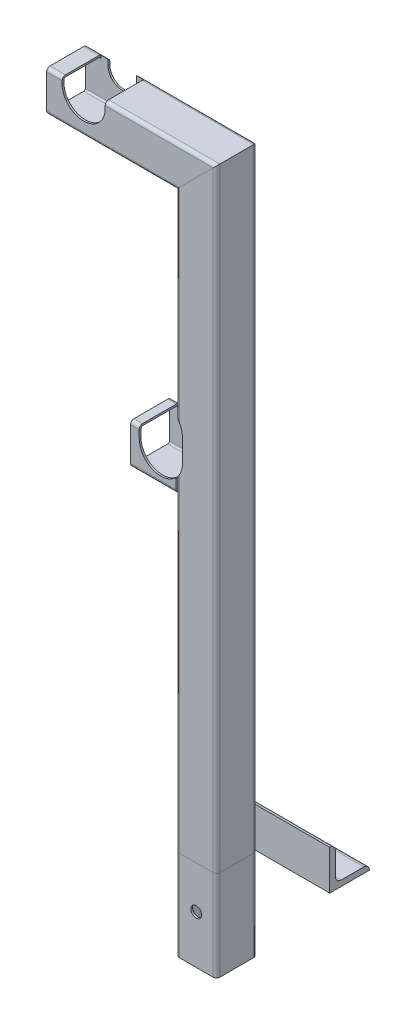
SolidWorks part; units mm, degrees
ref_plane "Front Plane" through (0, 0, 0) normal (0, 0, 1) x (1, 0, 0)
ref_plane "Top Plane" through (0, 0, 0) normal (0, 1, 0) x (1, 0, 0)
ref_plane "Right Plane" through (0, 0, 0) normal (1, 0, 0) x (0, 0, -1)
sketch "Sketch1" plane through (0, 0, 0) normal (0, 0, 1) x (1, 0, 0)
  line L0 (361.4375, 0) -> (361.4375, 524)
  line L1 (361.4375, 524) -> (229.3375, 524)
  line L2 (361.4375, 0) -> (361.4375, -80)
  line L3 (343.5375, 157.0549) -> (343.5375, -80) construction
  line L4 (348.3, 157.0549) -> (348.3, -80) construction
  line L5 (361.4375, 157.0549) -> (361.4375, -80) construction
  line L6 (361.4375, 291.4) -> (303.5375, 291.4)
  dimension "D1" = 524
  dimension "D2" = 80
  dimension "D3" = 132.1
  dimension "D4" = 4.7625
  dimension "D5" = 17.9
  dimension "D6" = 348.3
  dimension "D7" = 57.9
  dimension "D8" = 291.4
other "Structural MemberMain"
ref_plane "Plane1" through (361.4375, 0, 0) normal (0, 1, 0) x (-1, 0, 0)
sketch "Sketch11" plane through (361.4375, 0, 0) normal (0, 1, 0) x (-1, 0, 0)
  line L0 (-14.9, 16.3) -> (14.9, 16.3)
  line L1 (-14.9, 17.9) -> (14.9, 17.9)
  line L2 (-17.9, 14.9) -> (-17.9, -14.9)
  line L3 (-14.9, -17.9) -> (14.9, -17.9)
  line L4 (17.9, 14.9) -> (17.9, -14.9)
  line L5 (-17.9, 17.9) -> (17.9, -17.9) construction
  line L6 (-17.9, -17.9) -> (17.9, 17.9) construction
  line L7 (16.3, 14.9) -> (16.3, -14.9)
  line L8 (-14.9, -16.3) -> (14.9, -16.3)
  line L9 (-16.3, 14.9) -> (-16.3, -14.9)
  arc A0 (-17.9, -14.9) -> (-14.9, -17.9) centre (-14.9, -14.9) ccw
  arc A1 (14.9, -17.9) -> (17.9, -14.9) centre (14.9, -14.9) ccw
  arc A2 (17.9, 14.9) -> (14.9, 17.9) centre (14.9, 14.9) ccw
  arc A3 (-14.9, 17.9) -> (-17.9, 14.9) centre (-14.9, 14.9) ccw
  arc A4 (16.3, 14.9) -> (14.9, 16.3) centre (14.9, 14.9) ccw
  arc A5 (14.9, -16.3) -> (16.3, -14.9) centre (14.9, -14.9) ccw
  arc A6 (-16.3, -14.9) -> (-14.9, -16.3) centre (-14.9, -14.9) ccw
  arc A7 (-14.9, 16.3) -> (-16.3, 14.9) centre (-14.9, 14.9) ccw
  point P0 (0, 0)
  point P30 (0, 0)
  dimension "D3" = 3
  dimension "D1" = 35.8
  dimension "D2" = 35.8
  dimension "D4" = 1.6
sketch "Sketch12" plane through (0, 0, 0) normal (0, 0, 1) x (1, 0, 0)
  line L1 (262, 536.7) -> (262, 547.1) construction
  line L2 (249.3, 536.7) -> (249.3, 547.1)
  line L3 (274.7, 536.7) -> (274.7, 547.1)
  line L4 (361.4375, 524) -> (229.3375, 524) construction
  line L5 (229.3375, 541.9) -> (379.3375, 541.9) construction
  arc A0 (249.3, 536.7) -> (274.7, 536.7) centre (262, 536.7) ccw
  arc A1 (274.7, 547.1) -> (249.3, 547.1) centre (262, 547.1) ccw
  point P2 (262, 541.9)
  dimension "D1" = 25.4
  dimension "D2" = 262
extrude "Cut-ExtrudeTopRailGuide" cut sketch "Sketch12" against normal through all and the other way through all
sketch "Sketch13" plane through (0, 0, 0) normal (0, 1, 0) x (1, 0, 0)
  line L0 (343.5375, 17.9) -> (443.5375, 17.9)
  line L1 (343.5375, -14.9) -> (343.5375, 14.9) construction
  line L2 (274.7, 17.9) -> (376.3375, 17.9) construction
  point P4 (393.5375, 17.9)
  dimension "D1" = 100
other "Structural MemberAngle"
ref_plane "Plane2" through (343.5375, 0, -17.9) normal (1, 0, 0) x (0, 0, -1)
sketch "Sketch14" plane through (343.5375, 0, -17.9) normal (1, 0, 0) x (0, 0, -1)
  line L0 (0, 0) -> (0, 35)
  line L1 (0, 17.5) -> (5, 17.5) construction
  line L2 (5, 30) -> (5, 10)
  line L3 (10, 5) -> (30, 5)
  line L4 (17.5, 5) -> (17.5, 0) construction
  line L5 (35, 0) -> (0, 0)
  arc A0 (35, 0) -> (30, 5) centre (30, 0) ccw
  arc A1 (0, 35) -> (5, 30) centre (0, 30) cw
  arc A2 (10, 5) -> (5, 10) centre (10, 10) cw
  point P10 (17.5, 0)
  point P14 (0, 17.5)
  point P15 (5, 17.5)
  point P16 (17.5, 5)
  point P17 (5, 35)
  point P18 (35, 5)
  point P21 (0, 0)
  dimension "D2" = 5
  dimension "D3" = 35
  dimension "Radius_1" = 5
  dimension "D1" = 5
sketch "Sketch15" plane through (0, 0, 0) normal (0, 1, 0) x (1, 0, 0)
  line L0 (343.5375, 17.9) -> (443.5375, 17.9) construction
  line L2 (-65.8005, 37.9) -> (724.4755, 37.9) construction
  line L4 (0, 28.933) -> (0, -28.933) construction
  circle A0 centre (312.8, 37.9) radius 4.7625 construction
  circle A1 centre (348.3, 37.9) radius 5.0441 construction
  circle A2 centre (375, 37.9) radius 4.7625
  circle A3 centre (410, 37.9) radius 4.7625
  point P7 (329.3375, 37.9)
  point P16 (0, 0)
  dimension "D2" = 9.525
  dimension "D1" = 20
  dimension "D3" = 348.3
  dimension "D4" = 35.5
  dimension "D5" = 35
  dimension "D6" = 410
extrude "Cut-ExtrudeMountingHoles" cut sketch "Sketch15" along normal through all
sketch "Sketch16" plane through (0, 0, 0) normal (0, 0, 1) x (1, 0, 0)
  line L4 (281.05, 536.7) -> (281.05, 547.1)
  line L5 (242.95, 547.1) -> (242.95, 536.7)
  line L6 (281.05, 536.7) -> (281.05, 547.1)
  line L7 (242.95, 547.1) -> (242.95, 536.7)
  arc A4 (242.95, 536.7) -> (281.05, 536.7) centre (262, 536.7) ccw
  arc A5 (281.05, 547.1) -> (242.95, 547.1) centre (262, 547.1) ccw
  arc A6 (242.95, 536.7) -> (281.05, 536.7) centre (262, 536.7) ccw
  arc A7 (281.05, 547.1) -> (242.95, 547.1) centre (262, 547.1) ccw
  dimension "D1" = 6.35
extrude "Cut-ExtrudeEnlargeRailGuide" cut sketch "Sketch16" against normal up to surface and the other way through all up to face at (278.6938, 529.3125, -16.3)
sketch "Sketch17" plane through (0, 0, -17.9) normal (0, 0, 1) x (1, 0, 0)
  line L0 (330.2, 304.1) -> (330.2, 314.5) construction
  line L1 (317.5, 304.1) -> (317.5, 314.5)
  line L2 (342.9, 304.1) -> (342.9, 314.5)
  line L3 (303.5375, 309.3) -> (343.5375, 309.3) construction
  line L4 (361.4375, 291.4) -> (303.5375, 291.4) construction
  arc A0 (317.5, 304.1) -> (342.9, 304.1) centre (330.2, 304.1) ccw
  arc A1 (342.9, 314.5) -> (317.5, 314.5) centre (330.2, 314.5) ccw
  point P2 (330.2, 309.3)
  dimension "D1" = 25.4
  dimension "D2" = 12.7
  dimension "D3" = 330.2
extrude "Cut-Extrude1" cut sketch "Sketch17" along normal through all
sketch "Sketch18" plane through (0, 0, 17.9) normal (0, 0, 1) x (1, 0, 0)
  line L3 (330.2, 319.3) -> (330.2, 299.3) construction
  line L4 (349.3, 319.3) -> (349.3, 299.3)
  line L7 (311.1, 319.3) -> (311.1, 299.3)
  line L8 (330.2, 304.1) -> (330.2, 314.5) construction
  line L9 (303.5375, 309.3) -> (317.5, 309.3) construction
  arc A3 (349.3, 319.3) -> (311.1, 319.3) centre (330.2, 319.3) ccw
  arc A4 (311.1, 299.3) -> (349.3, 299.3) centre (330.2, 299.3) ccw
  point P2 (330.2, 309.3)
  dimension "D1" = 19.1
  dimension "D2" = 10
extrude "Cut-Extrude2" cut sketch "Sketch18" against normal up to surface (34.2 mm away)
sketch "Sketch19" plane through (0, 0, 17.9) normal (0, 0, 1) x (1, 0, 0)
  line L0 (361.4375, 0) -> (361.4375, -80) construction
  line L1 (343.5375, 0) -> (443.5375, 0) construction
  line L2 (379.3375, 0) -> (379.3375, -80) construction
  circle A0 centre (361.4375, -37.5) radius 4.7625
  dimension "D1" = 9.525
  dimension "D3" = 17.9
  dimension "D2" = 37.5
extrude "Cut-Extrude3" cut sketch "Sketch19" against normal through all
